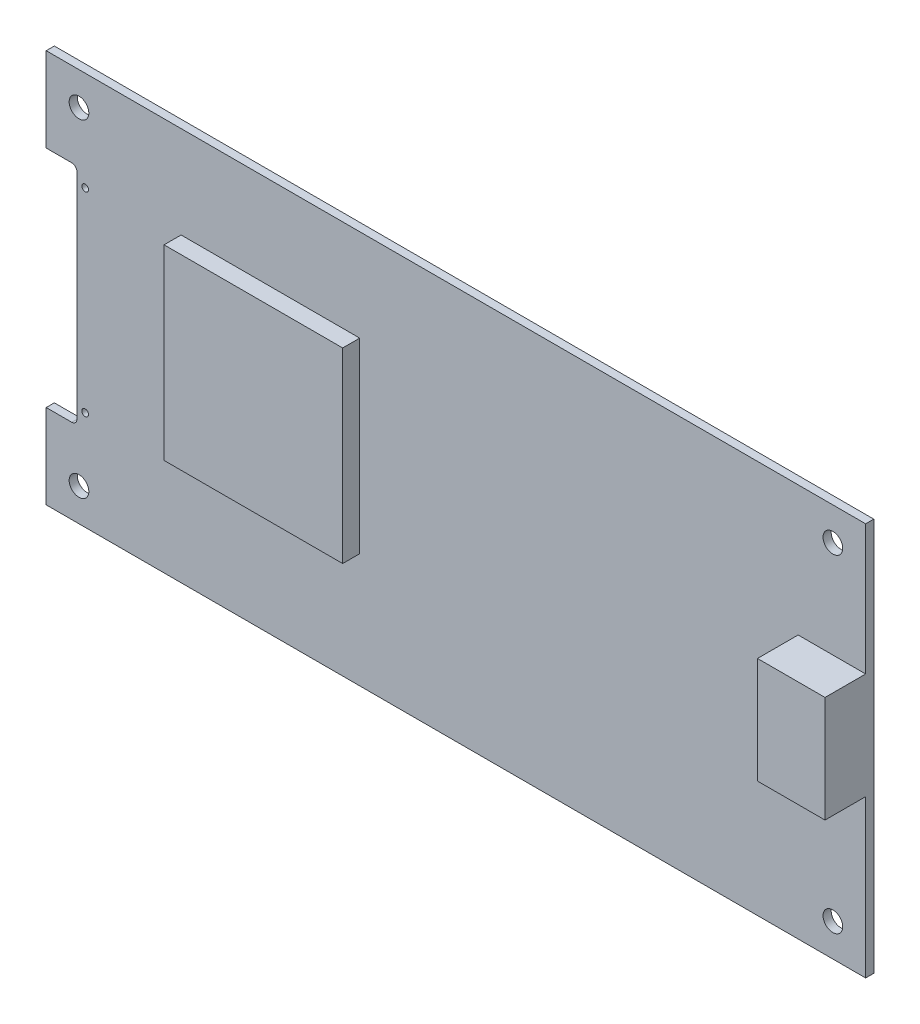
SolidWorks part; units mm, degrees
ref_plane "Front" through (0, 0, 0) normal (0, 0, 1) x (1, 0, 0)
ref_plane "Top" through (0, 0, 0) normal (0, 1, 0) x (1, 0, 0)
ref_plane "Right" through (0, 0, 0) normal (1, 0, 0) x (0, 0, -1)
sketch "Sketch1" plane through (0, 0, 0) normal (0, 0, 1) x (1, 0, 0)
  line L1 (0, 0) -> (158.75, 0)
  line L2 (0, 0) -> (0, -76.2)
  line L3 (0, -76.2) -> (158.75, -76.2)
  line L4 (158.75, 0) -> (158.75, -76.2)
  dimension "D1" = 158.75
  dimension "D2" = 76.2
extrude "Extrude1" add sketch "Sketch1" along normal blind 1.5748
sketch "Sketch2" plane through (0, 0, 1.5748) normal (0, 0, 1) x (1, 0, 0)
  line L0 (158.75, -76.2) -> (158.75, 0) construction
  line L1 (158.75, 0) -> (0, 0) construction
  line L2 (0, 0) -> (0, -76.2) construction
  line L3 (0, -76.2) -> (158.75, -76.2) construction
  circle A0 centre (152.4, -6.35) radius 1.905
  circle A1 centre (6.35, -6.35) radius 1.905
  circle A2 centre (152.4, -69.85) radius 1.905
  circle A3 centre (6.35, -69.85) radius 1.905
  dimension "D1" = 6.35
  dimension "D5" = 3.81
  dimension "D6" = 3.81
  dimension "D11" = 3.81
  dimension "D12" = 3.81
  dimension "D2" = 6.35
  dimension "D3" = 6.35
  dimension "D4" = 6.35
  dimension "D7" = 6.35
  dimension "D8" = 6.35
  dimension "D9" = 6.35
  dimension "D10" = 6.35
extrude "Cut-Extrude2" cut sketch "Sketch2" against normal blind 1.5748
sketch "Sketch4" plane through (0, 0, 1.5748) normal (0, 0, 1) x (1, 0, 0)
  line L0 (0, -76.2) -> (158.75, -76.2) construction
  line L1 (0, 0) -> (0, -76.2) construction
  line L2 (158.75, 0) -> (0, 0) construction
  line L3 (0, -16.335) -> (4.95, -16.335)
  line L4 (5.95, -58.865) -> (5.95, -17.335)
  line L5 (0, -16.335) -> (0, -59.865)
  line L6 (0, -59.865) -> (4.95, -59.865)
  circle A0 centre (7.55, -19.2349) radius 0.65
  circle A1 centre (7.55, -56.9651) radius 0.65
  arc A2 (4.95, -16.335) -> (5.95, -17.335) centre (4.95, -17.335) cw
  arc A3 (5.95, -58.865) -> (4.95, -59.865) centre (4.95, -58.865) cw
  dimension "D1" = 1.3
  dimension "D2" = 1.3
  dimension "D10" = 1
  dimension "D11" = 1
  dimension "D3" = 19.2349
  dimension "D4" = 7.55
  dimension "D5" = 19.2349
  dimension "D6" = 7.55
  dimension "D7" = 37.7302
  dimension "D8" = 43.53
  dimension "D9" = 5.95
  dimension "D12" = 16.335
  dimension "D13" = 16.335
extrude "Cut-Extrude3" cut sketch "Sketch4" against normal blind 1.5748
sketch "Sketch5" plane through (0, 0, 1.5748) normal (0, 0, 1) x (1, 0, 0)
  line L1 (26.134, -17.8508) -> (60.7346, -17.8508)
  line L2 (26.134, -17.8508) -> (26.134, -54.0241)
  line L3 (26.134, -54.0241) -> (60.7346, -54.0241)
  line L4 (60.7346, -17.8508) -> (60.7346, -54.0241)
extrude "Extrude2" add sketch "Sketch5" along normal blind 3.302
sketch "Sketch6" plane through (0, 0, 1.5748) normal (0, 0, 1) x (1, 0, 0)
  line L0 (158.75, -76.2) -> (158.75, 0) construction
  line L1 (145.669, -25.1932) -> (158.75, -25.1932)
  line L2 (145.669, -25.1932) -> (145.669, -45.7672)
  line L3 (145.669, -45.7672) -> (158.75, -45.7672)
  line L4 (158.75, -25.1932) -> (158.75, -45.7672)
  dimension "D1" = 13.081
  dimension "D2" = 20.574
extrude "Extrude3" add sketch "Sketch6" along normal blind 7.874
